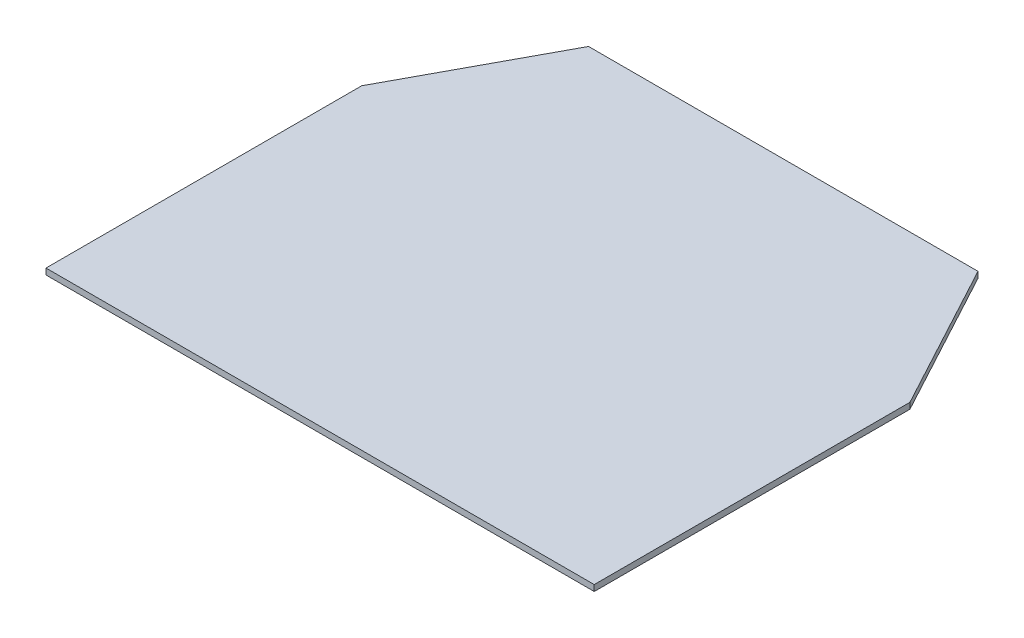
SolidWorks part; units mm, degrees
ref_plane "Front Plane" through (0, 0, 0) normal (0, 0, 1) x (1, 0, 0)
ref_plane "Top Plane" through (0, 0, 0) normal (0, 1, 0) x (1, 0, 0)
ref_plane "Right Plane" through (0, 0, 0) normal (1, 0, 0) x (0, 0, -1)
sketch "Sketch1" plane through (0, 0, 0) normal (0, 1, 0) x (1, 0, 0)
  line L0 (0, 0) -> (0, 167)
  line L1 (0, 167) -> (42, 245)
  line L2 (42, 245) -> (248, 245)
  line L3 (248, 245) -> (290, 167)
  line L4 (290, 167) -> (290, 0)
  line L5 (290, 0) -> (0, 0)
  dimension "D1" = 290
  dimension "D2" = 245
  dimension "D3" = 78
  dimension "D4" = 206
extrude "Boss-Extrude1" add sketch "Sketch1" along normal blind 3.2
